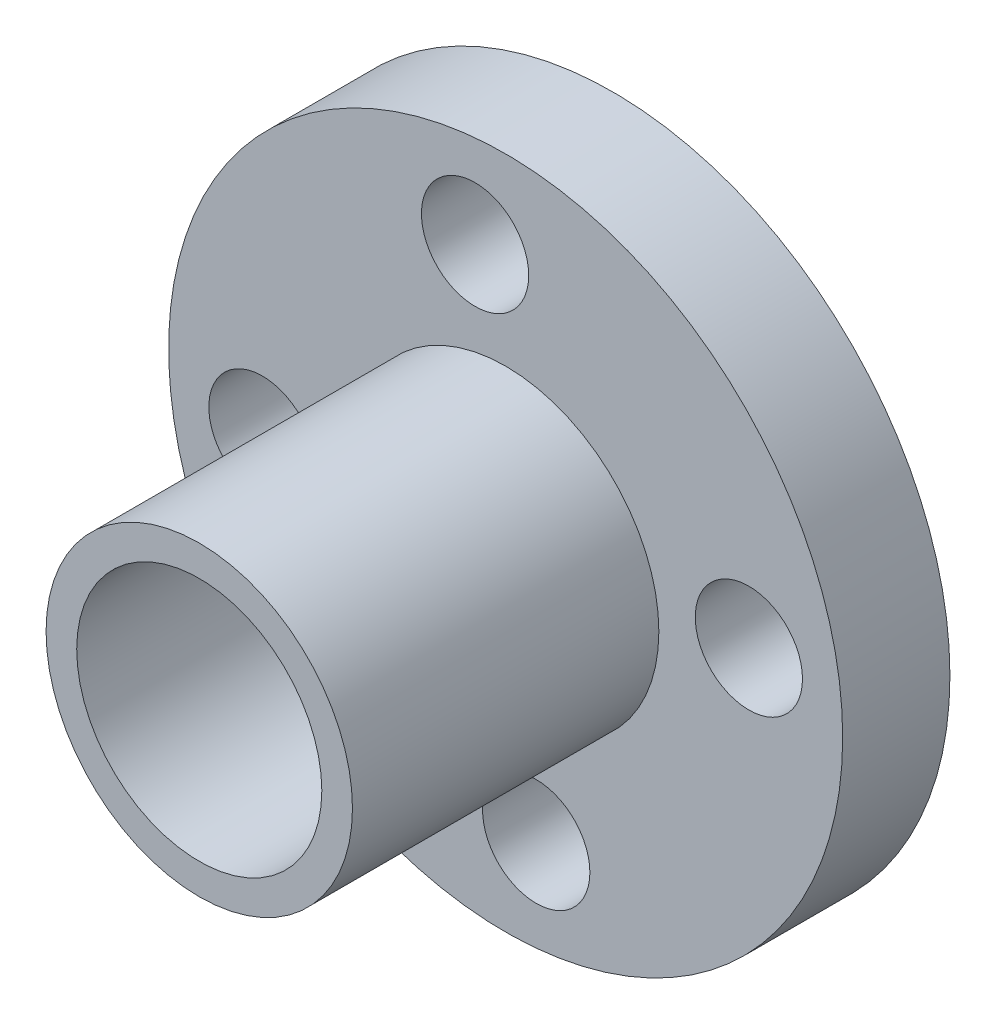
SolidWorks part; units mm, degrees
ref_plane "前视基准面" through (0, 0, 0) normal (0, 0, 1) x (1, 0, 0)
ref_plane "上视基准面" through (0, 0, 0) normal (0, 1, 0) x (1, 0, 0)
ref_plane "右视基准面" through (0, 0, 0) normal (1, 0, 0) x (0, 0, -1)
sketch "草图1" plane through (0, 0, 0) normal (0, 0, 1) x (1, 0, 0)
  circle A0 centre (0, 0) radius 11
  dimension "D1" = 22
extrude "凸台-拉伸1" add sketch "草图1" along normal blind 3.5
sketch "草图2" plane through (0, 0, 3.5) normal (0, 0, 1) x (1, 0, 0)
  circle A0 centre (0, 0) radius 5
extrude "凸台-拉伸2" add sketch "草图2" along normal blind 10 and the other way blind 5
sketch "草图3" plane through (0, 0, 13.5) normal (0, 0, 1) x (1, 0, 0)
  circle A0 centre (0, 0) radius 4
extrude "切除-拉伸1" cut sketch "草图3" against normal through all
sketch "草图4" plane through (0, 0, 3.5) normal (0, 0, 1) x (1, 0, 0)
  circle A0 centre (-0.9987, 7.9374) radius 1.75
  circle A1 centre (7.9374, 0.9987) radius 1.75
  circle A2 centre (0.9987, -7.9374) radius 1.75
  circle A3 centre (-7.9374, -0.9987) radius 1.75
  point P12 (0, 0)
  dimension "D1" = 8
  dimension "D2" = 4
extrude "切除-拉伸2" cut sketch "草图4" against normal through all
sketch "草图5" plane through (0, 0, 3.5) normal (0, 0, 1) x (1, 0, 0)
  line L0 (-7.9374, -0.9987) -> (7.9374, 0.9987) construction
